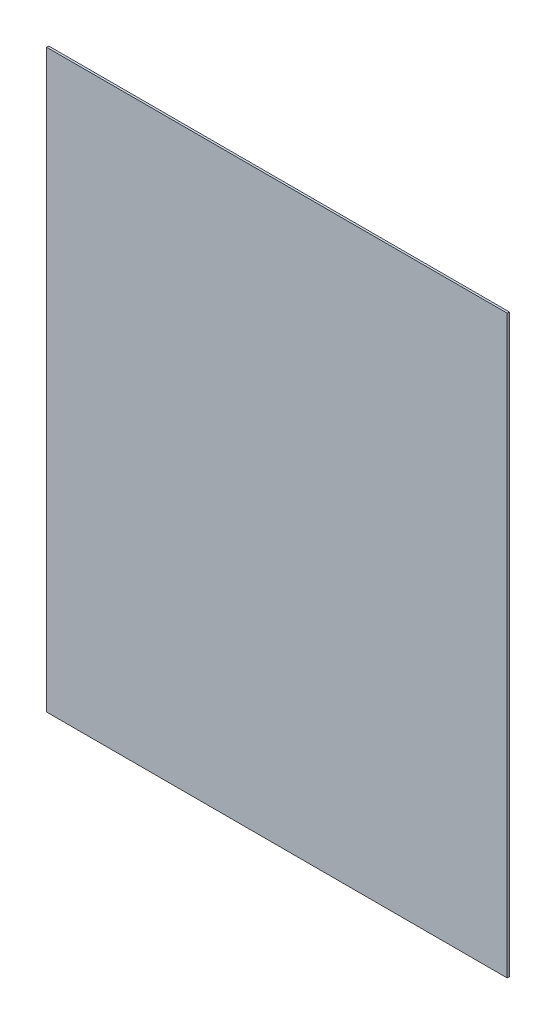
SolidWorks part; units mm, degrees
material "Verre"
ref_plane "Plan de face" through (0, 0, 0) normal (0, 0, 1) x (1, 0, 0)
ref_plane "Plan de dessus" through (0, 0, 0) normal (0, 1, 0) x (1, 0, 0)
ref_plane "Plan de droite" through (0, 0, 0) normal (1, 0, 0) x (0, 0, -1)
sketch "Esquisse1" plane through (0, 0, 0) normal (0, 0, 1) x (1, 0, 0)
  line L1 (0, 0) -> (-640, 0)
  line L2 (0, 0) -> (0, 800)
  line L3 (0, 800) -> (-640, 800)
  line L4 (-640, 0) -> (-640, 800)
  dimension "D1" = 800
  dimension "D2" = 640
extrude "Boss.-Extru.1" add sketch "Esquisse1" along normal blind 3
